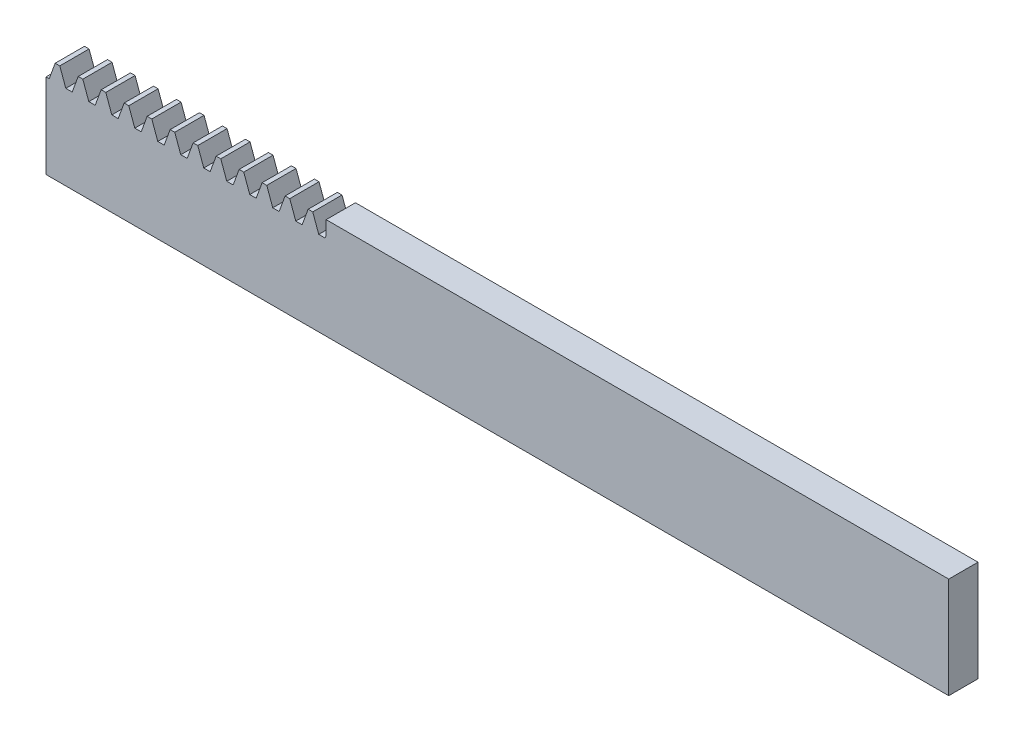
SolidWorks part; units mm, degrees
extrude "Blank" add sketch "BlankSke" against normal blind 6
sketch "BlankSke" plane through (0, 0, 0) normal (0, 0, 1) x (1, 0, 0)
  line L1 (0, 0) -> (185, 0)
  line L2 (0, 0) -> (0, 21.7)
  line L3 (0, 21.7) -> (185, 21.7)
  line L4 (185, 0) -> (185, 21.7)
  dimension "Length" = 185
  dimension "Blank_height" = 21.7
ref_plane "Plane1" through (0, 0, 0) normal (0, 0, 1) x (1, 0, 0)
ref_plane "Plane2" through (0, 0, 0) normal (0, 1, 0) x (1, 0, 0)
ref_plane "Plane3" through (0, 0, 0) normal (1, 0, 0) x (0, 0, -1)
sketch "HoldingSke" plane through (0, 0, 0) normal (0, 1, 0) x (1, 0, 0)
  line L0 (0, 0) -> (0.0928, 0.6602)
  line L1 (-15, 0) -> (100, 0) construction
  line L2 (0, 0) -> (-2.1039, 2.3779)
  line L3 (0, 0) -> (-11.863, 4.5341)
  line L4 (0, 0) -> (6.5177, 5.6657)
  line L5 (0, 0) -> (-23.7986, -8.8762)
  line L6 (0, 0) -> (-10.5278, -7.1032)
  line L9 (-71.009, 38.7566) -> (102.8342, 102.0303)
  line L10 (-76.2, 3.8779) -> (-56, 3.8779)
  line L11 (0, 0) -> (-6, 0)
  line L12 (-76.2, 101.6) -> (-76.147, 101.6)
  line L13 (24.9733, 27.94) -> (52.9518, 28.4284)
  line L14 (24.9733, 27.94) -> (24.9743, 27.94)
  line L15 (24.9733, 27.94) -> (100.4006, 29.5858)
  circle A0 centre (0, 0) radius 19.05
  circle A1 centre (0, 0) radius 10.1
  circle A2 centre (0, 0) radius 12.7
  dimension "MPH" = 20.2
  dimension "Diameter" = 38.1
  dimension "Num_teeth" = 41
  dimension "Pitch" = 0.6667
  dimension "Show_teeth" = 998
  dimension "Thickness" = 12.7
  dimension "Ap" = 20
  dimension "Pitch_height" = 20.2
  dimension "Width" = 6
  dimension "Backlash" = 0.053
  dimension "Addendum_fac" = 1
  dimension "Dedendum_fac" = 1.25
  dimension "Clearance_fac" = 0.25
  dimension "Dedendum_add" = 0.001
  dimension "Length" = 185
  dimension "Module" = 1.5
sketch "TooCutSkeIll" plane through (0, 0, 0) normal (0, 0, 1) x (1, 0, 0)
  line L0 (-1.8687, 21.6605) -> (-0.7447, 18.5724)
  line L1 (-0.3914, 18.325) -> (0.3914, 18.325)
  line L2 (0.7447, 18.5724) -> (1.8687, 21.6605)
  line L3 (185, 21.7) -> (0, 21.7) construction
  line L4 (0, 0) -> (0, 64.897) construction
  line L5 (-13.208, 20.2) -> (12.954, 20.2) construction
  line L6 (0, 0) -> (185, 0) construction
  line L7 (1.3371, 20.2) -> (1.3371, 48.7463) construction
  line L8 (-1.3371, 20.2) -> (-1.3371, 48.7463) construction
  line L9 (1.9251, 21.7) -> (1.9251, 21.7254)
  line L10 (-1.9251, 21.7) -> (-1.9251, 21.7254)
  line L11 (-1.9251, 21.7254) -> (1.9251, 21.7254)
  arc A0 (0.3914, 18.325) -> (0.7447, 18.5724) centre (0.3914, 18.701) ccw
  arc A1 (-0.7447, 18.5724) -> (-0.3914, 18.325) centre (-0.3914, 18.701) ccw
  arc A2 (1.9251, 21.7) -> (1.8687, 21.6605) centre (1.9251, 21.64) ccw
  arc A3 (-1.8687, 21.6605) -> (-1.9251, 21.7) centre (-1.9251, 21.64) ccw
  dimension "Pitch_height" = 20.2
  dimension "Addendum_plus" = 1.5254
  dimension "Pressure_angle" = 20
  dimension "Gap_width" = 2.6742
  dimension "Dedendum" = 1.875
extrude "ToothCutIll" [suppressed] cut sketch "TooCutSkeIll" against normal through all
sketch "TooCutSkeSim" plane through (0, 0, 0) normal (0, 0, 1) x (1, 0, 0)
  line L0 (0.6547, 18.325) -> (-0.6547, 18.325)
  line L1 (1.8923, 21.7254) -> (0.6547, 18.325)
  line L2 (0, 17.4625) -> (0, 53.467) construction
  line L3 (1.8923, 21.7254) -> (-1.8923, 21.7254)
  line L6 (-1.8923, 21.7254) -> (-0.6547, 18.325)
  line L9 (-1.3371, 20.2) -> (1.3371, 20.2) construction
  line L10 (0, 0) -> (185, 0) construction
  line L11 (1.3371, 20.2) -> (1.3371, 53.467) construction
  line L12 (-1.3371, 20.2) -> (-1.3371, 53.467) construction
  dimension "Pitch_height" = 20.2
  dimension "Addendum_plus" = 1.5254
  dimension "Pressure_angle" = 20
  dimension "Gap_width" = 2.6742
  dimension "Dedendum" = 1.875
extrude "ToothCutSim" cut sketch "TooCutSkeSim" against normal through all
pattern_linear "TeethCuts" count 40 spacing 4.7124 along (1, 0, 0) of "ToothCutIll", "ToothCutSim"
sketch "Esquisse2" plane through (0, 0, 0) normal (0, 0, 1) x (1, 0, 0)
  line L1 (57.4148, 21.7) -> (185, 21.7)
  line L2 (57.4148, 21.7) -> (57.4148, 18.325)
  line L3 (57.4148, 18.325) -> (185, 18.325)
  line L4 (185, 21.7) -> (185, 18.325)
  line L5 (74.7436, 18.325) -> (76.0529, 18.325) construction
  line L6 (74.7436, 18.325) -> (76.0529, 18.325) construction
  line L7 (59.378, 21.7) -> (58.4317, 21.7) construction
  line L8 (185, 0) -> (185, 19.8696) construction
  point P4 (75.3982, 18.325)
extrude "Boss.-Extru.1" add sketch "Esquisse2" against normal blind 6
sketch "Esquisse3" plane through (0, 0, 0) normal (0, 0, 1) x (1, 0, 0)
  line L0 (185, 0) -> (185, 21.7) construction
  line L1 (0, 0) -> (185, 0)
  line L2 (0, 0) -> (0, 1)
  line L3 (0, 1) -> (185, 1)
  line L4 (185, 0) -> (185, 1)
  dimension "D1" = 1
extrude "Enlèv. mat.-Extru.1" cut sketch "Esquisse3" against normal blind 6
equation "' \"Module@HoldingSke\" = 6.35"
equation "' \"Num_teeth@HoldingSke\" = 12"
equation "' \"Ap@HoldingSke\" =  20"
equation "' \"Ap@HoldingSke\" = 20"
equation "' \"Width@HoldingSke\" = 0.25 * 25.4"
equation "' \"Show_teeth@HoldingSke\" = 500"
equation "' \"Backlash@HoldingSke\" = 0.009 * 25.4"
equation "' \"Addendum_fac@HoldingSke\" = 1.0"
equation "' \"Dedendum_fac@HoldingSke\" = 1.25"
equation "' \"Dedendum_add@HoldingSke\" = 0.00005 * 25.4"
equation "' \"Clearance_fac@HoldingSke\" = 0.25"
equation "' \"Pitch_height@HoldingSke\" = 1 * 25.4"
equation "' \"Length@HoldingSke\" = 4.71 * 25.4"
equation "\"Pitch@HoldingSke\" = 1 / \"Module@HoldingSke\""
equation "\"MPH@HoldingSke\" = \"Dedendum_fac@HoldingSke\" / \"Pitch@HoldingSke\" + 2 * \"Dedendum_add@HoldingSke\" + 0.002 * 25.4"
equation "\"MPH@HoldingSke\" = ((sgn( \"MPH@HoldingSke\" - \"Pitch_height@HoldingSke\")+1)*( \"MPH@HoldingSke\" - \"Pitch_height@HoldingSke\"))/2 + \"Pitch_height@HoldingSke\""
equation "\"Blank_height@BlankSke\" = \"Pitch_height@HoldingSke\" + \"Addendum_fac@HoldingSke\"  / \"Pitch@HoldingSke\" "
equation "\"Length@BlankSke\" =  \"Length@HoldingSke\""
equation "\"Face_width@Blank\" = \"Width@HoldingSke\""
equation "\"Pressure_angle@TooCutSkeIll\" = \"Ap@HoldingSke\""
equation "\"Addendum_plus@TooCutSkeIll\" =  \"Addendum_fac@HoldingSke\"  / \"Pitch@HoldingSke\" + 0.001 *25.4"
equation "\"Dedendum@TooCutSkeIll\" = \"Dedendum_fac@HoldingSke\"  / \"Pitch@HoldingSke\""
equation "\"Pitch_height@TooCutSkeIll\" =  \"MPH@HoldingSke\""
equation "\"Gap_width@TooCutSkeIll\" = 3.14159265 / 2 / \"Pitch@HoldingSke\" + 6 * \"Backlash@HoldingSke\""
equation "\"Pressure_angle@TooCutSkeSim\" = \"Ap@HoldingSke\""
equation "\"Addendum_plus@TooCutSkeSim\" =  \"Addendum_fac@HoldingSke\"  / \"Pitch@HoldingSke\" + 0.001 * 25.4"
equation "\"Dedendum@TooCutSkeSim\" = \"Dedendum_fac@HoldingSke\"  / \"Pitch@HoldingSke\""
equation "\"Pitch_height@TooCutSkeSim\" =  \"MPH@HoldingSke\""
equation "\"Gap_width@TooCutSkeSim\" = 3.14159265 / 2 / \"Pitch@HoldingSke\" + 6 * \"Backlash@HoldingSke\""
equation "\"Root_fillet@TooCutSkeIll\" = \"Clearance_fac@HoldingSke\" / \"Pitch@HoldingSke\" + \"Dedendum_add@HoldingSke\""
equation "\"Break_rad@TooCutSkeIll\" = 0.02 / \"Pitch@HoldingSke\" * 2"
equation "\"Linear_pitch@TeethCuts\" = 3.14159265 / \"Pitch@HoldingSke\""
equation "\"Num_teeth@HoldingSke\" = int( ( \"Length@HoldingSke\" + 0 ) / (3.14159265 / \"Pitch@HoldingSke\")) + 0.9999  + 1"
equation " \"Num_teeth@TeethCuts\" = int( \"Show_teeth@HoldingSke\" ) + 1"
equation " \"Num_teeth@TeethCuts\" = ((sgn( \"Num_teeth@TeethCuts\" - \"Num_teeth@HoldingSke\" )-1)*( \"Num_teeth@TeethCuts\" - \"Num_teeth@HoldingSke\" ))/-2+ \"Num_teeth@HoldingSke\""
equation " \"Num_teeth@TeethCuts\" = ((sgn( \"Num_teeth@TeethCuts\" - 2.0)+1)*( \"Num_teeth@TeethCuts\" - 2.0))/2 +2.0"
